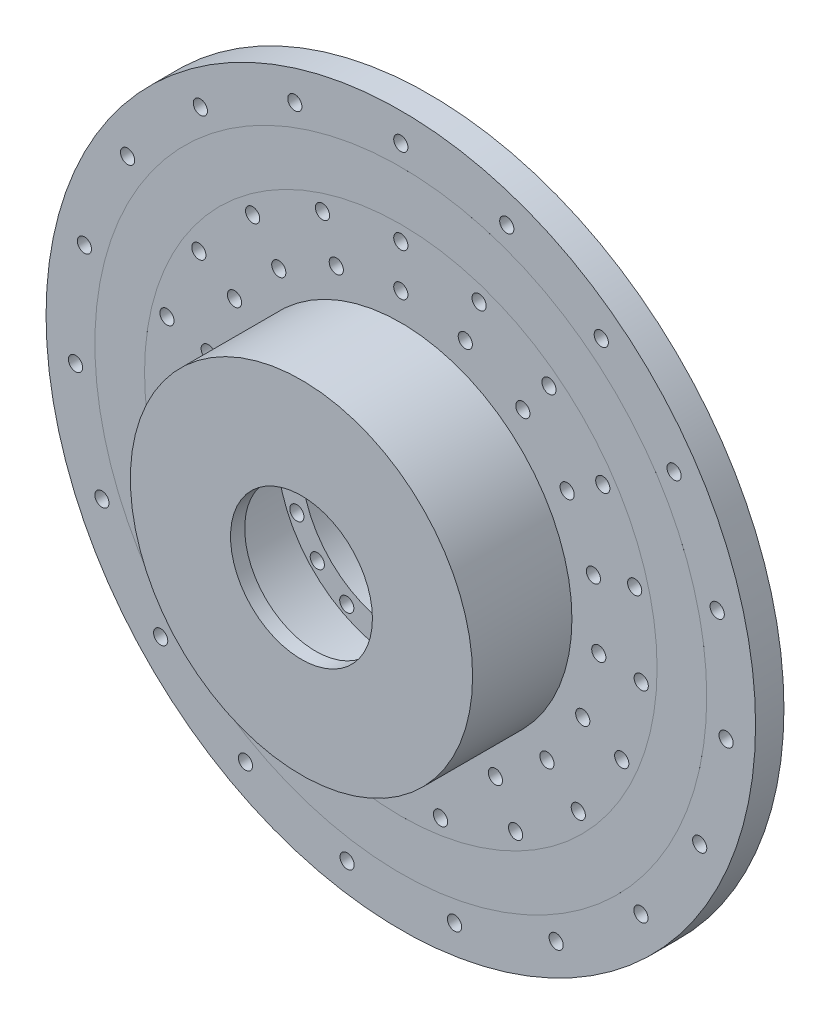
SolidWorks part; units mm, degrees
ref_plane "Front Plane" through (0, 0, 0) normal (0, 0, 1) x (1, 0, 0)
ref_plane "Top Plane" through (0, 0, 0) normal (0, 1, 0) x (1, 0, 0)
ref_plane "Right Plane" through (0, 0, 0) normal (1, 0, 0) x (0, 0, -1)
sketch "Sketch1" plane through (0, 0, 0) normal (0, 0, 1) x (1, 0, 0)
  circle A0 centre (0, 0) radius 125
  circle A1 centre (0, 0) radius 35
  circle A2 centre (0, 40) radius 2.5
  circle A3 centre (0, 55) radius 2.5
  circle A4 centre (0, 70) radius 2.5
  circle A5 centre (0, 85) radius 2.5
  circle A6 centre (0, 100) radius 2.5
  circle A9 centre (0, 115) radius 2.5
  circle A12 centre (37.3404, 108.769) radius 2.5
  circle A13 centre (32.4699, 94.5817) radius 2.5
  circle A14 centre (27.5995, 80.3945) radius 2.5
  circle A15 centre (22.729, 66.2072) radius 2.5
  circle A16 centre (17.8585, 52.0199) radius 2.5
  circle A17 centre (12.988, 37.8327) radius 2.5
  circle A19 centre (70.6345, 90.7512) radius 2.5
  circle A20 centre (61.4213, 78.9141) radius 2.5
  circle A21 centre (52.2081, 67.0769) radius 2.5
  circle A22 centre (42.9949, 55.2398) radius 2.5
  circle A23 centre (33.7817, 43.4027) radius 2.5
  circle A24 centre (24.5685, 31.5656) radius 2.5
  circle A26 centre (96.2741, 62.899) radius 2.5
  circle A27 centre (83.7166, 54.6948) radius 2.5
  circle A28 centre (71.1592, 46.4906) radius 2.5
  circle A29 centre (58.6017, 38.2864) radius 2.5
  circle A30 centre (46.0442, 30.0821) radius 2.5
  circle A31 centre (33.4867, 21.8779) radius 2.5
  circle A33 centre (111.481, 28.2308) radius 2.5
  circle A34 centre (96.94, 24.5485) radius 2.5
  circle A35 centre (82.399, 20.8663) radius 2.5
  circle A36 centre (67.858, 17.184) radius 2.5
  circle A37 centre (53.317, 13.5017) radius 2.5
  circle A38 centre (38.776, 9.8194) radius 2.5
  circle A40 centre (114.6072, -9.4966) radius 2.5
  circle A41 centre (99.6584, -8.2579) radius 2.5
  circle A42 centre (84.7097, -7.0192) radius 2.5
  circle A43 centre (69.7609, -5.7806) radius 2.5
  circle A44 centre (54.8121, -4.5419) radius 2.5
  circle A45 centre (39.8634, -3.3032) radius 2.5
  circle A47 centre (105.3139, -46.195) radius 2.5
  circle A48 centre (91.5773, -40.1695) radius 2.5
  circle A49 centre (77.8407, -34.1441) radius 2.5
  circle A50 centre (64.1041, -28.1187) radius 2.5
  circle A51 centre (50.3675, -22.0932) radius 2.5
  circle A52 centre (36.6309, -16.0678) radius 2.5
  circle A54 centre (84.6082, -77.8874) radius 2.5
  circle A55 centre (73.5724, -67.7282) radius 2.5
  circle A56 centre (62.5365, -57.5689) radius 2.5
  circle A57 centre (51.5007, -47.4097) radius 2.5
  circle A58 centre (40.4648, -37.2505) radius 2.5
  circle A59 centre (29.429, -27.0913) radius 2.5
  circle A61 centre (54.734, -101.1395) radius 2.5
  circle A62 centre (47.5947, -87.9474) radius 2.5
  circle A63 centre (40.4555, -74.7553) radius 2.5
  circle A64 centre (33.3163, -61.5632) radius 2.5
  circle A65 centre (26.1771, -48.3711) radius 2.5
  circle A66 centre (19.0379, -35.179) radius 2.5
  circle A68 centre (18.9284, -113.4315) radius 2.5
  circle A69 centre (16.4595, -98.6361) radius 2.5
  circle A70 centre (13.9905, -83.8407) radius 2.5
  circle A71 centre (11.5216, -69.0453) radius 2.5
  circle A72 centre (9.0527, -54.2499) radius 2.5
  circle A73 centre (6.5838, -39.4545) radius 2.5
  circle A75 centre (-18.9284, -113.4315) radius 2.5
  circle A76 centre (-16.4595, -98.6361) radius 2.5
  circle A77 centre (-13.9905, -83.8407) radius 2.5
  circle A78 centre (-11.5216, -69.0453) radius 2.5
  circle A79 centre (-9.0527, -54.2499) radius 2.5
  circle A80 centre (-6.5838, -39.4545) radius 2.5
  circle A82 centre (-54.734, -101.1395) radius 2.5
  circle A83 centre (-47.5947, -87.9474) radius 2.5
  circle A84 centre (-40.4555, -74.7553) radius 2.5
  circle A85 centre (-33.3163, -61.5632) radius 2.5
  circle A86 centre (-26.1771, -48.3711) radius 2.5
  circle A87 centre (-19.0379, -35.179) radius 2.5
  circle A89 centre (-84.6082, -77.8874) radius 2.5
  circle A90 centre (-73.5724, -67.7282) radius 2.5
  circle A91 centre (-62.5365, -57.5689) radius 2.5
  circle A92 centre (-51.5007, -47.4097) radius 2.5
  circle A93 centre (-40.4648, -37.2505) radius 2.5
  circle A94 centre (-29.429, -27.0913) radius 2.5
  circle A96 centre (-105.3139, -46.195) radius 2.5
  circle A97 centre (-91.5773, -40.1695) radius 2.5
  circle A98 centre (-77.8407, -34.1441) radius 2.5
  circle A99 centre (-64.1041, -28.1187) radius 2.5
  circle A100 centre (-50.3675, -22.0932) radius 2.5
  circle A101 centre (-36.6309, -16.0678) radius 2.5
  circle A103 centre (-114.6072, -9.4966) radius 2.5
  circle A104 centre (-99.6584, -8.2579) radius 2.5
  circle A105 centre (-84.7097, -7.0192) radius 2.5
  circle A106 centre (-69.7609, -5.7806) radius 2.5
  circle A107 centre (-54.8121, -4.5419) radius 2.5
  circle A108 centre (-39.8634, -3.3032) radius 2.5
  circle A110 centre (-111.481, 28.2308) radius 2.5
  circle A111 centre (-96.94, 24.5485) radius 2.5
  circle A112 centre (-82.399, 20.8663) radius 2.5
  circle A113 centre (-67.858, 17.184) radius 2.5
  circle A114 centre (-53.317, 13.5017) radius 2.5
  circle A115 centre (-38.776, 9.8194) radius 2.5
  circle A117 centre (-96.2741, 62.899) radius 2.5
  circle A118 centre (-83.7166, 54.6948) radius 2.5
  circle A119 centre (-71.1592, 46.4906) radius 2.5
  circle A120 centre (-58.6017, 38.2864) radius 2.5
  circle A121 centre (-46.0442, 30.0821) radius 2.5
  circle A122 centre (-33.4867, 21.8779) radius 2.5
  circle A124 centre (-70.6345, 90.7512) radius 2.5
  circle A125 centre (-61.4213, 78.9141) radius 2.5
  circle A126 centre (-52.2081, 67.0769) radius 2.5
  circle A127 centre (-42.9949, 55.2398) radius 2.5
  circle A128 centre (-33.7817, 43.4027) radius 2.5
  circle A129 centre (-24.5685, 31.5656) radius 2.5
  circle A131 centre (-37.3404, 108.769) radius 2.5
  circle A132 centre (-32.4699, 94.5817) radius 2.5
  circle A133 centre (-27.5995, 80.3945) radius 2.5
  circle A134 centre (-22.729, 66.2072) radius 2.5
  circle A135 centre (-17.8585, 52.0199) radius 2.5
  circle A136 centre (-12.988, 37.8327) radius 2.5
  circle A137 centre (0, 130) radius 2.5 [skipped]
  point P272 (0, 0)
  dimension "D1" = 40
  dimension "D3" = 70
  dimension "D5" = 5
  dimension "D4" = 7
  dimension "D6" = 19
extrude "Boss-Extrude1" add sketch "Sketch1" along normal blind 10
sketch "Sketch2" plane through (0, 0, 10) normal (0, 0, 1) x (1, 0, 0)
  circle A0 centre (0, 0) radius 43.5883
  circle A1 centre (0, 0) radius 60.2958
extrude "Boss-Extrude2" add sketch "Sketch2" along normal blind 30
sketch "Sketch3" plane through (0, 0, 40) normal (0, 0, 1) x (1, 0, 0)
  circle A0 centre (0, 0) radius 60.2958
extrude "Boss-Extrude3" add sketch "Sketch3" along normal blind 5
sketch "Sketch4" plane through (0, 0, 40) normal (0, 0, -1) x (-1, 0, 0)
  circle A0 centre (0, 0) radius 25
  dimension "D1" = 50
extrude "Cut-Extrude2" cut sketch "Sketch4" against normal mid plane 95
sketch "Sketch5" plane through (0, 0, 0) normal (0, 0, 1) x (1, 0, 0)
  circle A0 centre (0, 0) radius 90.2986
  circle A1 centre (0, 0) radius 107.7961
extrude "Boss-Extrude4" add sketch "Sketch5" along normal blind 10.001 and the other way blind 0.001
